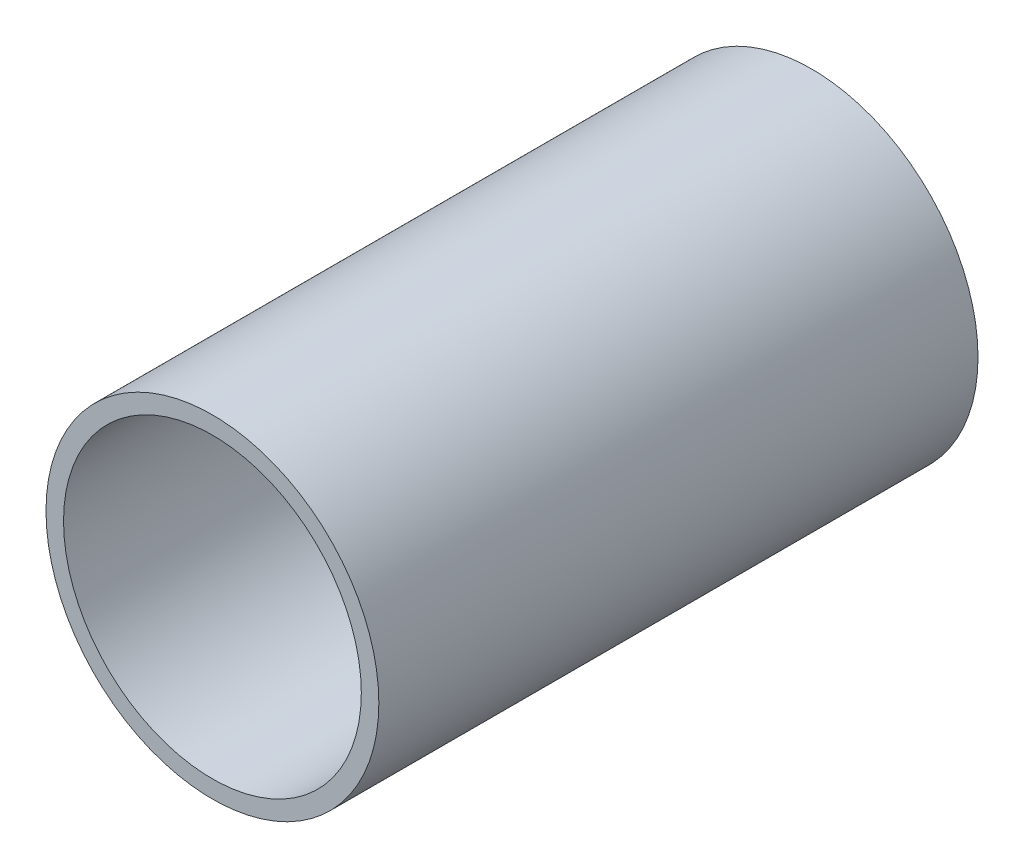
SolidWorks part; units mm, degrees
material "PVC Rigid"
ref_plane "Front Plane" through (0, 0, 0) normal (0, 0, 1) x (1, 0, 0)
ref_plane "Top Plane" through (0, 0, 0) normal (0, 1, 0) x (1, 0, 0)
ref_plane "Right Plane" through (0, 0, 0) normal (1, 0, 0) x (0, 0, -1)
sketch "Sketch1" plane through (0, 0, 0) normal (0, 0, 1) x (1, 0, 0)
  circle A0 centre (0, 0) radius 57.15
  dimension "Pipe OD" = 114.3
extrude "Extrude-Thin1" add sketch "Sketch1" along normal mid plane 205.75 thin thin type one direction reverse wall 6.0198
